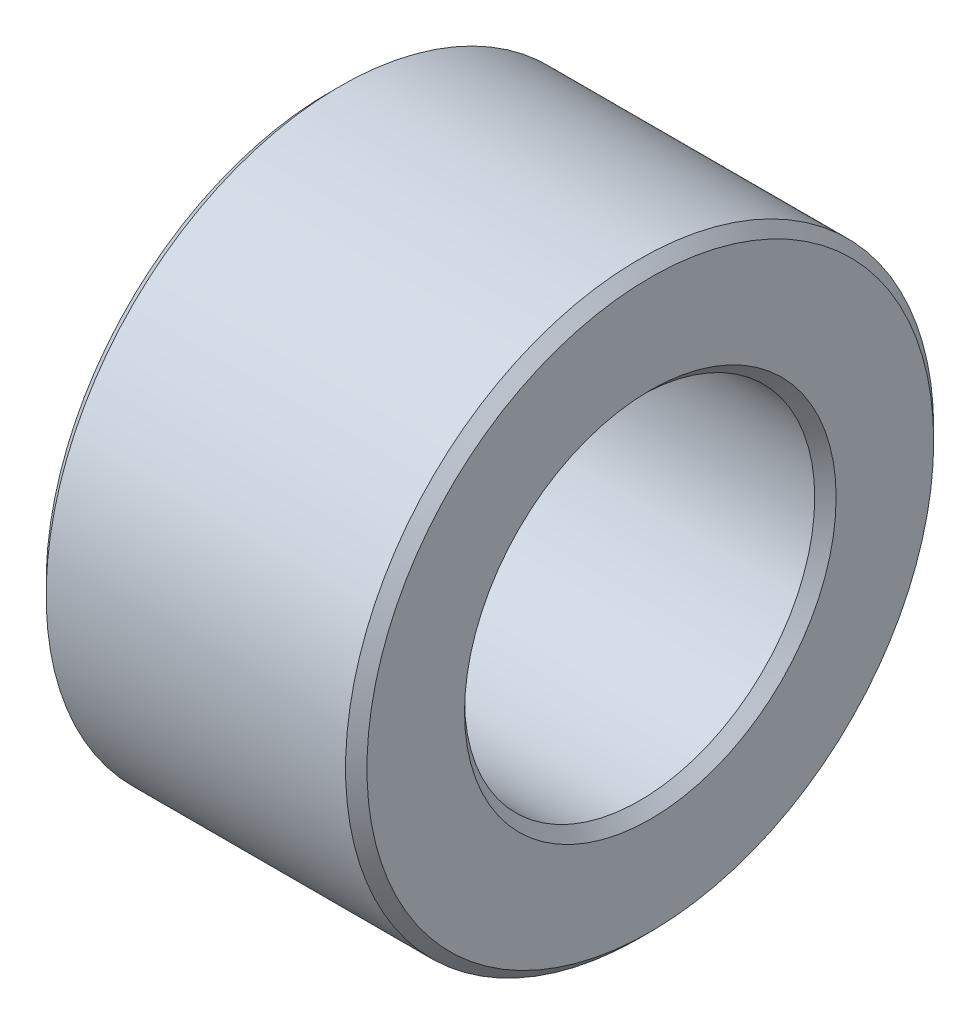
SolidWorks part; units mm, degrees
material "MS-4340"
ref_plane "Front Plane" through (0, 0, 0) normal (0, 0, 1) x (1, 0, 0)
ref_plane "Top Plane" through (0, 0, 0) normal (0, 1, 0) x (1, 0, 0)
ref_plane "Right Plane" through (0, 0, 0) normal (1, 0, 0) x (0, 0, -1)
sketch "Sketch1" plane through (0, 0, 0) normal (1, 0, 0) x (0, 0, -1)
  circle A0 centre (0, 0) radius 55
  circle A1 centre (0, 0) radius 30
  dimension "D1" = 110
  dimension "D2" = 60
extrude "Extrude1" add sketch "Sketch1" against normal mid plane 60
sketch "Sketch2" plane through (0, 0, 0) normal (1, 0, 0) x (0, 0, -1)
  circle A0 centre (0, 0) radius 32.75
  dimension "D1" = 65.5
extrude "Machine" cut sketch "Sketch2" against normal mid plane 60
chamfer "Chamfer-Outer" distance 2 angle 45 2 edges at (-30, 0, -55) (30, 0, -55)
chamfer "Chamfer-Inner" distance 2 angle 45 2 edges at (-30, 0, -32.75) (30, 0, -32.75)
